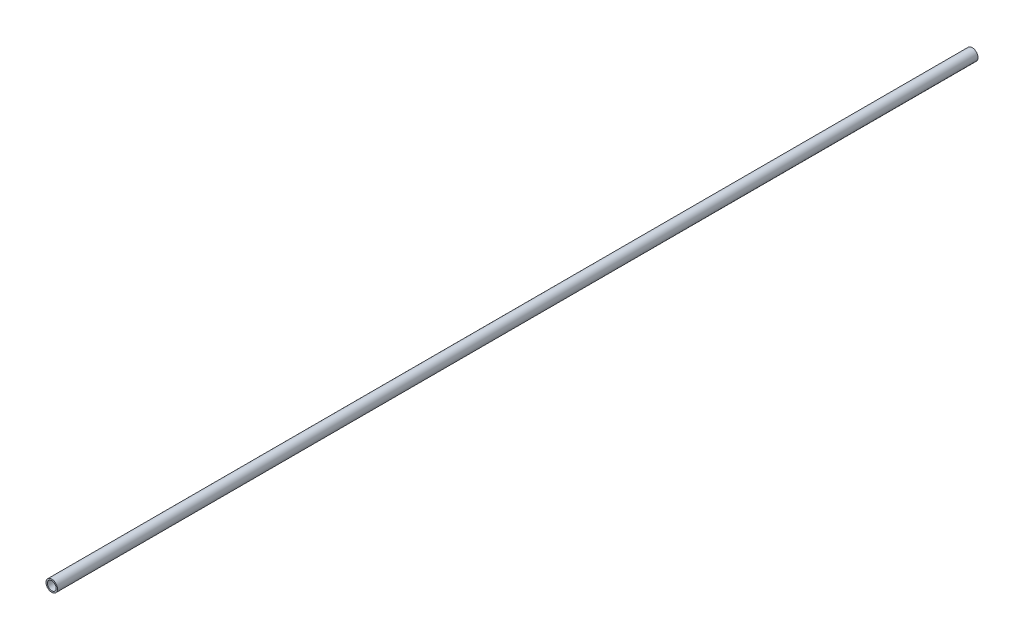
SolidWorks part; units mm, degrees
material "AISI 316 Barra de acero inoxidable recocido (SS)"
ref_plane "Alzado" through (0, 0, 0) normal (0, 0, 1) x (1, 0, 0)
ref_plane "Planta" through (0, 0, 0) normal (0, 1, 0) x (1, 0, 0)
ref_plane "Vista lateral" through (0, 0, 0) normal (1, 0, 0) x (0, 0, -1)
sketch "Croquis1" plane through (0, 0, 0) normal (0, 0, 1) x (1, 0, 0)
  circle A0 centre (0, 0) radius 12.5
  circle A1 centre (0, 0) radius 9.5
  dimension "D1" = 25
  dimension "D2" = 19
extrude "Saliente-Extruir1" add sketch "Croquis1" along normal blind 2000 and the other way blind 3 from offset 0
